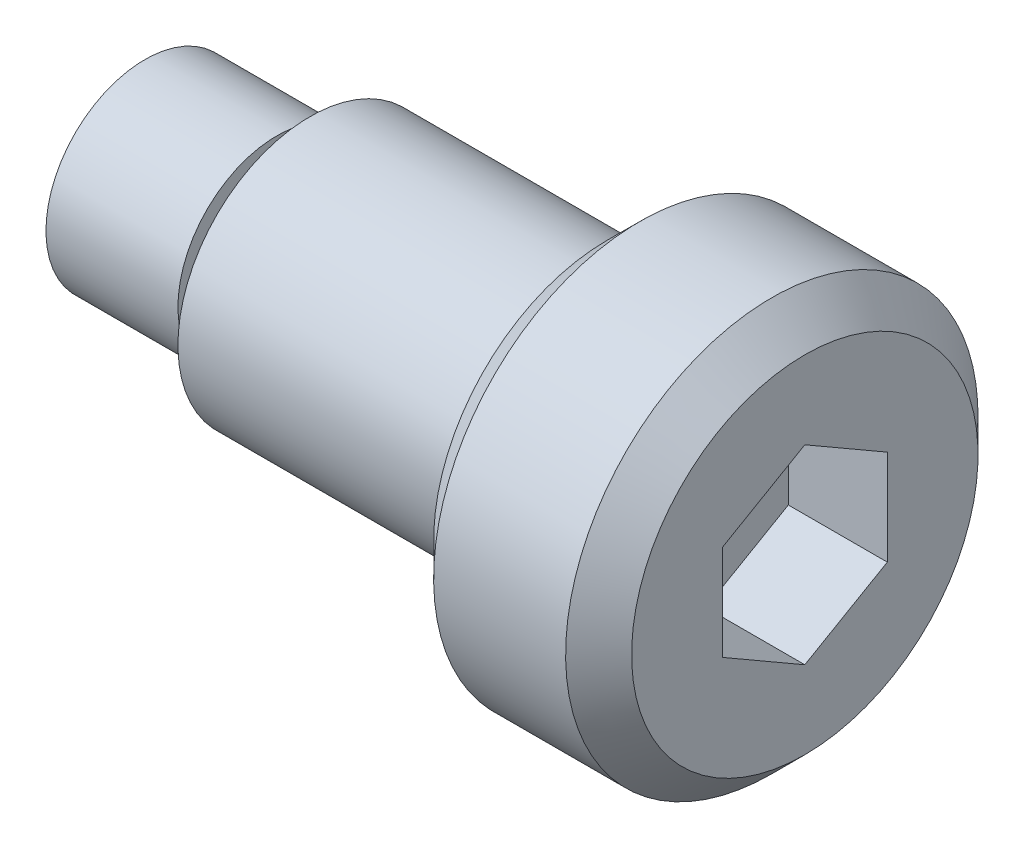
SolidWorks part; units mm, degrees
material "AISI 1020"
ref_plane "Front Plane" through (0, 0, 0) normal (0, 0, 1) x (1, 0, 0)
ref_plane "Top Plane" through (0, 0, 0) normal (0, 1, 0) x (1, 0, 0)
ref_plane "Right Plane" through (0, 0, 0) normal (1, 0, 0) x (0, 0, -1)
sketch "Sketch1" plane through (0, 0, 0) normal (0, 0, 1) x (1, 0, 0)
  line L0 (-20, 0) -> (20, 0) construction
  line L1 (-20, 0) -> (-20, 6)
  line L2 (-20, 6) -> (-12, 6)
  line L3 (-12, 6) -> (-12, 5)
  line L4 (-12, 5) -> (-10, 5)
  line L5 (-10, 5) -> (-10, 8)
  line L6 (-10, 8) -> (8, 8)
  line L7 (8, 8) -> (8, 10.5)
  line L8 (10, 12.5) -> (18, 12.5)
  line L9 (20, 10.5) -> (20, 0)
  line L10 (8, 10.5) -> (10, 12.5)
  line L11 (18, 12.5) -> (20, 10.5)
  line L12 (-20, 0) -> (20, 0)
  point P3 (0, 0)
  point P4 (8, 12.5)
  point P11 (20, 12.5)
  dimension "D1" = 40
  dimension "D2" = 8
  dimension "D3" = 10
  dimension "D4" = 28
  dimension "D5" = 12
  dimension "D6" = 16
  dimension "D7" = 10
  dimension "D8" = 25
  dimension "D9" = 2
  dimension "D10" = 45
  dimension "D11" = 2
  dimension "D12" = 45
revolve "Revolve1" add sketch "Sketch1" angle 360 about L0
cosmetic thread "Cosmetic Thread1" parameters "D1"=8, "D2"=10.072
sketch "Sketch2" plane through (20, 0, 0) normal (1, 0, 0) x (0, 0, -1)
  line L1 (0, 5.7735) -> (-5, 2.8868)
  line L2 (-5, 2.8868) -> (-5, -2.8868)
  line L3 (-5, -2.8868) -> (0, -5.7735)
  line L4 (0, -5.7735) -> (5, -2.8868)
  line L5 (5, -2.8868) -> (5, 2.8868)
  line L6 (5, 2.8868) -> (0, 5.7735)
  circle A0 centre (0, 0) radius 5 construction
  dimension "D1" = 10
extrude "Cut-Extrude1" cut sketch "Sketch2" against normal blind 6 and the other way through all
